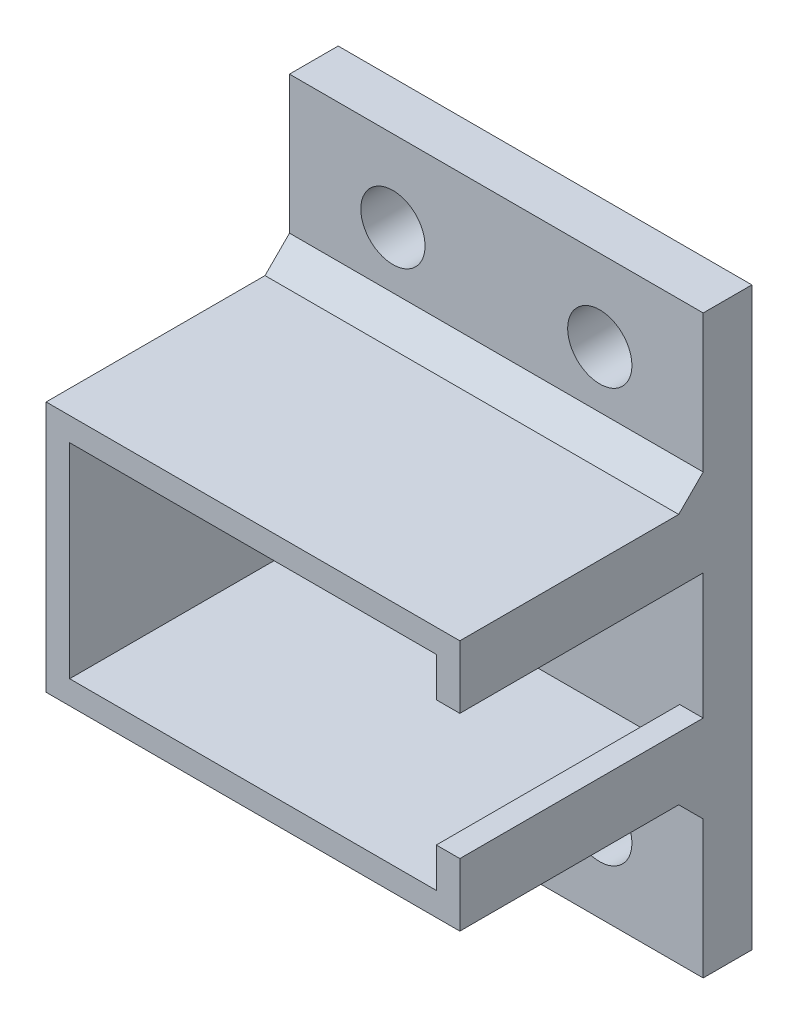
SolidWorks part; units mm, degrees
ref_plane "Front Plane" through (0, 0, 0) normal (0, 0, 1) x (1, 0, 0)
ref_plane "Top Plane" through (0, 0, 0) normal (0, 1, 0) x (1, 0, 0)
ref_plane "Right Plane" through (0, 0, 0) normal (1, 0, 0) x (0, 0, -1)
sketch "Sketch3" plane through (0, 0, 0) normal (0, 0, 1) x (1, 0, 0)
  line L0 (0, 0) -> (0, 15.5)
  line L1 (0, 0) -> (25.5, 0)
  line L2 (0, 15.5) -> (25.5, 15.5)
  line L3 (25.5, 0) -> (25.5, 15.5)
extrude "Boss-Extrude2" add sketch "Sketch3" along normal blind 18
sketch "Sketch4" plane through (0, 0, 18) normal (0, 0, 1) x (1, 0, 0)
  line L0 (24.05, 14.05) -> (1.45, 14.05)
  line L1 (24.05, 14.05) -> (24.05, 1.45)
  line L2 (1.45, 14.05) -> (1.45, 1.45)
  line L3 (24.05, 1.45) -> (1.45, 1.45)
  point P7 (25.5, 7.75)
  point P18 (24.05, 7.75)
extrude "Cut-Extrude1" cut sketch "Sketch4" against normal blind 15
sketch "Sketch7" plane through (0, 0, 0) normal (0, -1, 0) x (1, 0, 0)
  line L1 (25.5, 18) -> (25.5, 0) construction
  line L3 (0, 0) -> (25.5, 0)
  line L4 (0, 0) -> (0, 3)
  line L6 (25.5, 0) -> (25.5, 3)
  line L7 (0, 3) -> (25.5, 3)
extrude "Boss-Extrude4" add sketch "Sketch7" against normal blind 25.5 and the other way blind 10
sketch "Sketch8" plane through (0, 0, 3) normal (0, 0, 1) x (1, 0, 0)
  circle A1 centre (19.125, 20.5) radius 1.98
  circle A2 centre (6.375, -5) radius 1.98
  circle A3 centre (6.375, 20.5) radius 1.98
  circle A4 centre (19.125, -5) radius 1.98
  point P3 (25.5, 20.5)
  point P9 (0, -5)
  point P16 (19.125, 20.5)
  point P23 (6.375, -5)
extrude "Cut-Extrude2" cut sketch "Sketch8" against normal blind 31 and the other way through all
sketch "Sketch9" plane through (0, 0, 0) normal (-1, 0, 0) x (0, 0, 1)
  line L0 (3, 17.01) -> (3, 15.5)
  line L1 (3, 17.01) -> (4.51, 15.5)
  line L2 (18, 15.5) -> (3, 15.5) construction
  line L3 (3, 15.5) -> (4.51, 15.5)
  line L4 (4.51, 0) -> (3, 0)
  line L5 (3, -1.51) -> (4.51, 0)
  line L6 (18, 0) -> (3, 0) construction
  line L7 (3, 0) -> (3, -1.51)
extrude "Boss-Extrude5" add sketch "Sketch9" against normal blind 25.5
sketch "Sketch10" plane through (25.5, 0, 0) normal (1, 0, 0) x (0, 0, -1)
  line L0 (-18, 3.875) -> (-18, 11.625)
  line L1 (-18, 11.625) -> (-3, 11.625)
  line L2 (-18, 7.75) -> (-18, 15.5) construction
  line L3 (-3, 1.45) -> (-3, 14.05) construction
  line L4 (-3, 11.625) -> (-3, 3.875)
  line L5 (-3, 3.875) -> (-18, 3.875)
  point P6 (-18, 7.75)
extrude "Cut-Extrude3" cut sketch "Sketch10" along normal blind 5 and the other way blind 9
